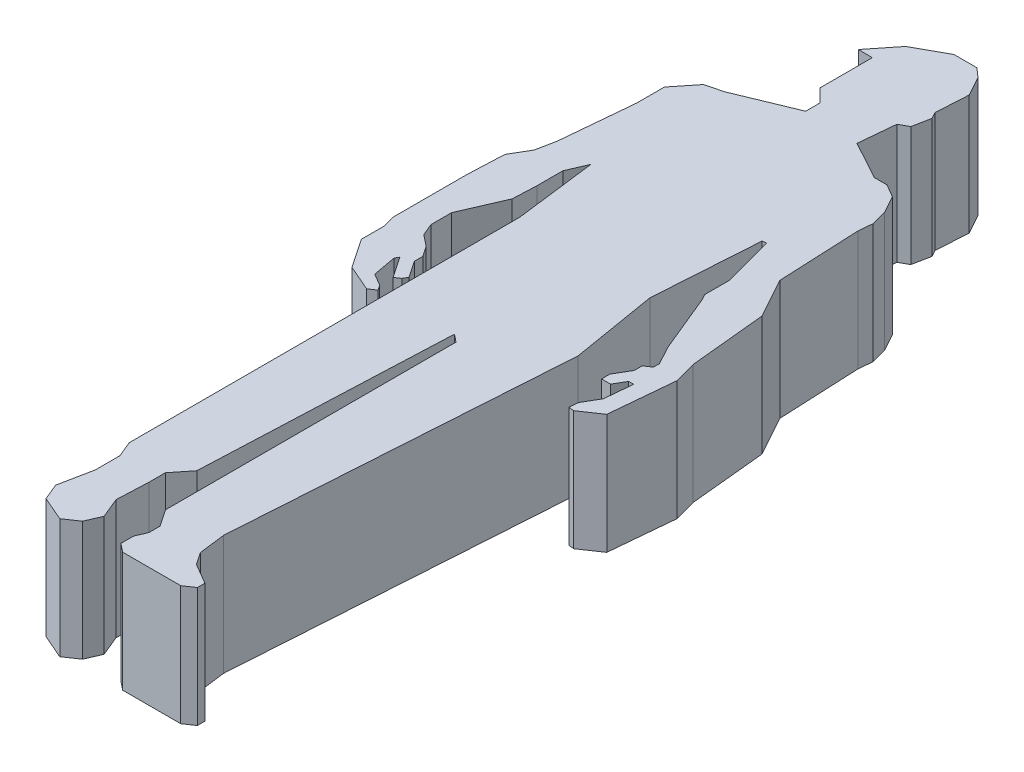
SolidWorks part; units mm, degrees
ref_plane "Front Plane" through (0, 0, 0) normal (0, 0, 1) x (1, 0, 0)
ref_plane "Top Plane" through (0, 0, 0) normal (0, 1, 0) x (1, 0, 0)
ref_plane "Right Plane" through (0, 0, 0) normal (1, 0, 0) x (0, 0, -1)
sketch "Sketch1" plane through (0, 0, 0) normal (0, 1, 0) x (1, 0, 0)
  line L0 (55, 316) -> (275, 316) construction
  line L1 (578.7014, 1825.2875) -> (531.1348, 1825.2875)
  line L2 (531.1348, 1825.2875) -> (465.9509, 1789.4658)
  line L3 (465.9509, 1789.4658) -> (421.9077, 1734.265)
  line L4 (421.9077, 1734.265) -> (451.2698, 1734.265)
  line L5 (451.2698, 1734.265) -> (451.2698, 1624.4507)
  line L6 (451.2698, 1624.4507) -> (478.5766, 1597.1439)
  line L7 (478.5766, 1597.1439) -> (478.5766, 1567.4881)
  line L8 (478.5766, 1567.4881) -> (359.0728, 1518.1598)
  line L9 (359.0728, 1518.1598) -> (323.251, 1508.7639)
  line L10 (323.251, 1508.7639) -> (287.1478, 1463.5146)
  line L11 (287.1478, 1463.5146) -> (287.1478, 1405.7151)
  line L12 (287.1478, 1405.7151) -> (273.108, 1253.8584)
  line L13 (273.108, 1253.8584) -> (265.025, 1213.4305)
  line L14 (265.025, 1213.4305) -> (242.3676, 1174.724)
  line L15 (242.3676, 1174.724) -> (239.0634, 1097.311)
  line L16 (239.0634, 1097.311) -> (239.0634, 944.8241)
  line L17 (239.0634, 944.8241) -> (245.8914, 918.7923)
  line L18 (245.8914, 918.7923) -> (245.8914, 871.1226)
  line L19 (245.8914, 871.1226) -> (287.1478, 810.2896)
  line L20 (287.1478, 810.2896) -> (341.1619, 786.8923)
  line L21 (341.1619, 786.8923) -> (355.4662, 796.5934)
  line L22 (355.4662, 796.5934) -> (348.314, 807.1394)
  line L23 (348.314, 807.1394) -> (323.251, 821.8104)
  line L24 (323.251, 821.8104) -> (314.1548, 871.1226)
  line L25 (314.1548, 871.1226) -> (318.7029, 878.8922)
  line L26 (318.7029, 878.8922) -> (348.314, 835.2303)
  line L27 (348.314, 835.2303) -> (359.0728, 842.5268)
  line L28 (359.0728, 842.5268) -> (364.6246, 852.0112)
  line L29 (364.6246, 852.0112) -> (341.1619, 886.6073)
  line L30 (341.1619, 886.6073) -> (341.1619, 904.3028)
  line L31 (341.1619, 904.3028) -> (326.5609, 925.832)
  line L32 (326.5609, 925.832) -> (302.7576, 944.8241)
  line L33 (302.7576, 944.8241) -> (292.1285, 970.5743)
  line L34 (292.1285, 970.5743) -> (292.1285, 1013.6769)
  line L35 (292.1285, 1013.6769) -> (330.422, 1102.0797)
  line L36 (330.422, 1102.0797) -> (332.5518, 1151.9794)
  line L37 (332.5518, 1151.9794) -> (332.5518, 1205.8078)
  line L38 (332.5518, 1205.8078) -> (350.2755, 1246.724)
  line L39 (350.2755, 1246.724) -> (371.6166, 1076.7859)
  line L40 (371.6166, 1076.7859) -> (371.6166, 895.4551)
  line L41 (371.6166, 895.4551) -> (371.6166, 260.0809)
  line L42 (371.6166, 260.0809) -> (385.4409, 226.5897)
  line L43 (385.4409, 226.5897) -> (385.4409, 175.3771)
  line L44 (385.4409, 175.3771) -> (371.6166, 106.2328)
  line L45 (371.6166, 106.2328) -> (385.8474, 71.7568)
  line L46 (385.8474, 71.7568) -> (436.5888, 49.7772)
  line L47 (436.5888, 49.7772) -> (464.9232, 68.9934)
  line L48 (464.9232, 68.9934) -> (478.5766, 100.513)
  line L49 (478.5766, 100.513) -> (460.9881, 143.1233)
  line L50 (460.9881, 143.1233) -> (463.8149, 209.351)
  line L51 (463.8149, 209.351) -> (463.8149, 243.3353)
  line L52 (463.8149, 243.3353) -> (493.0371, 279.9604)
  line L53 (493.0371, 279.9604) -> (515.0885, 796.5934)
  line L54 (515.0885, 796.5934) -> (531.1348, 783.7905)
  line L55 (531.1348, 783.7905) -> (531.1348, 176.2371)
  line L56 (531.1348, 176.2371) -> (554.9181, 141.1684)
  line L57 (554.9181, 141.1684) -> (554.9181, 117.6771)
  line L58 (554.9181, 117.6771) -> (545.299, 95.4708)
  line L59 (545.299, 95.4708) -> (545.299, 68.9934)
  line L60 (545.299, 68.9934) -> (562.9423, 54.9163)
  line L61 (562.9423, 54.9163) -> (684.3515, 54.9163)
  line L62 (684.3515, 54.9163) -> (705.1083, 68.9934)
  line L63 (705.1083, 68.9934) -> (705.1083, 84.7532)
  line L64 (705.1083, 84.7532) -> (662.2565, 109.8372)
  line L65 (662.2565, 109.8372) -> (645.0091, 135.2687)
  line L66 (645.0091, 135.2687) -> (637.9794, 191.2459)
  line L67 (637.9794, 191.2459) -> (683.6824, 886.6073)
  line L68 (683.6824, 886.6073) -> (653.6328, 1066.725)
  line L69 (653.6328, 1066.725) -> (668.0865, 1286.6351)
  line L70 (668.0865, 1286.6351) -> (676.5721, 1288.0508)
  line L71 (676.5721, 1288.0508) -> (705.0729, 1181.8095)
  line L72 (705.0729, 1181.8095) -> (705.0729, 1129.7757)
  line L73 (705.0729, 1129.7757) -> (711.8474, 1117.4484)
  line L74 (711.8474, 1117.4484) -> (762.5101, 994.7118)
  line L75 (762.5101, 994.7118) -> (782.8504, 957.6992)
  line L76 (782.8504, 957.6992) -> (782.8504, 944.8241)
  line L77 (782.8504, 944.8241) -> (768.8484, 935.3281)
  line L78 (768.8484, 935.3281) -> (768.8484, 918.7923)
  line L79 (768.8484, 918.7923) -> (750.0084, 886.6073)
  line L80 (750.0084, 886.6073) -> (750.0084, 869.3093)
  line L81 (750.0084, 869.3093) -> (768.8484, 869.3093)
  line L82 (768.8484, 869.3093) -> (782.8504, 893.2293)
  line L83 (782.8504, 893.2293) -> (793.2146, 893.2293)
  line L84 (793.2146, 893.2293) -> (787.8523, 835.2303)
  line L85 (787.8523, 835.2303) -> (768.8484, 802.7653)
  line L86 (768.8484, 802.7653) -> (767.0941, 783.7905)
  line L87 (767.0941, 783.7905) -> (778.3504, 782.7498)
  line L88 (778.3504, 782.7498) -> (819.5353, 810.6812)
  line L89 (819.5353, 810.6812) -> (831.9374, 944.8241)
  line L90 (831.9374, 944.8241) -> (819.5353, 991.0548)
  line L91 (819.5353, 991.0548) -> (803.8158, 1150.6715)
  line L92 (803.8158, 1150.6715) -> (757.8649, 1234.2869)
  line L93 (757.8649, 1234.2869) -> (750.0084, 1405.7151)
  line L94 (750.0084, 1405.7151) -> (752.6803, 1434.6149)
  line L95 (752.6803, 1434.6149) -> (743.9568, 1467.133)
  line L96 (743.9568, 1467.133) -> (724.0628, 1503.3337)
  line L97 (724.0628, 1503.3337) -> (697.0283, 1519.1587)
  line L98 (697.0283, 1519.1587) -> (670.6291, 1519.1587)
  line L99 (670.6291, 1519.1587) -> (590.4645, 1562.8918)
  line L100 (590.4645, 1562.8918) -> (597.5298, 1639.3117)
  line L101 (597.5298, 1639.3117) -> (616.2534, 1649.6013)
  line L102 (616.2534, 1649.6013) -> (623.6469, 1686.5808)
  line L103 (623.6469, 1686.5808) -> (616.2534, 1700.0346)
  line L104 (616.2534, 1700.0346) -> (620.1764, 1767.8394)
  line L105 (620.1764, 1767.8394) -> (597.5298, 1808.8928)
  line L106 (597.5298, 1808.8928) -> (578.7014, 1825.2875)
  point P75 (0, 0)
  point P109 (800.7986, 1149.0749)
  point P110 (807.3793, 1151.9794)
  point P111 (0, 0)
  point P112 (728.6319, 1076.7859)
  point P113 (705.0729, 1129.7757)
  point P114 (803.8158, 1150.6715)
extrude "Boss-Extrude1" add sketch "Sketch1" along normal blind 250
